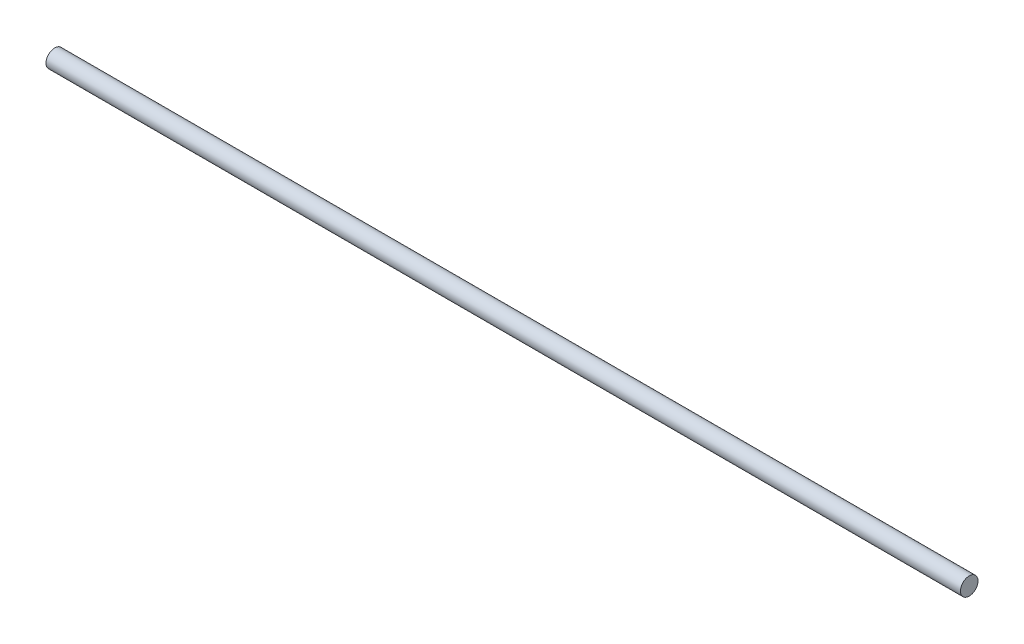
SolidWorks part; units mm, degrees
ref_plane "Front Plane" through (0, 0, 0) normal (0, 0, 1) x (1, 0, 0)
ref_plane "Top Plane" through (0, 0, 0) normal (0, 1, 0) x (1, 0, 0)
ref_plane "Right Plane" through (0, 0, 0) normal (1, 0, 0) x (0, 0, -1)
sketch "Sketch1" plane through (0, 0, 0) normal (1, 0, 0) x (0, 0, -1)
  circle A0 centre (0, 0) radius 4
extrude "Boss-Extrude1" add sketch "Sketch1" along normal blind 416.75
